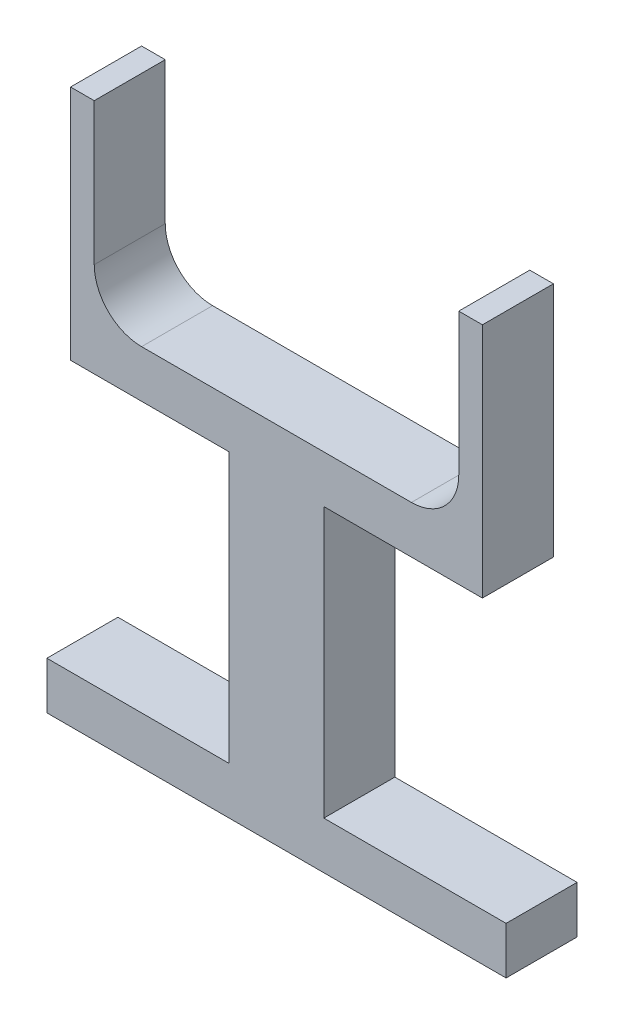
SolidWorks part; units mm, degrees
ref_plane "前基準面" through (0, 0, 0) normal (0, 0, 1) x (1, 0, 0)
ref_plane "上基準面" through (0, 0, 0) normal (0, 1, 0) x (1, 0, 0)
ref_plane "右基準面" through (0, 0, 0) normal (1, 0, 0) x (0, 0, -1)
sketch "草圖1" plane through (0, 0, 0) normal (0, 0, 1) x (1, 0, 0)
  line L1 (-77.3723, -11.2295) -> (19.6277, -11.2295)
  line L2 (-77.3723, -11.2295) -> (-77.3723, -21.2295)
  line L3 (-77.3723, -21.2295) -> (19.6277, -21.2295)
  line L4 (19.6277, -11.2295) -> (19.6277, -21.2295)
  line L5 (-38.8723, 45.7705) -> (-18.8723, 45.7705)
  line L6 (-38.8723, 45.7705) -> (-38.8723, -11.2295)
  line L7 (-38.8723, -11.2295) -> (-18.8723, -11.2295)
  line L8 (-18.8723, 45.7705) -> (-18.8723, -11.2295)
  line L9 (-72.3723, 55.7705) -> (14.6277, 55.7705)
  line L10 (-72.3723, 55.7705) -> (-72.3723, 45.7705)
  line L11 (-72.3723, 45.7705) -> (14.6277, 45.7705)
  line L12 (14.6277, 55.7705) -> (14.6277, 45.7705)
  line L13 (-72.3723, 55.7705) -> (-67.3723, 55.7705)
  line L14 (-72.3723, 55.7705) -> (-72.3723, 95.7705)
  line L15 (-72.3723, 95.7705) -> (-67.3723, 95.7705)
  line L16 (-67.3723, 55.7705) -> (-67.3723, 95.7705)
  line L17 (14.6277, 55.7705) -> (9.6277, 55.7705)
  line L18 (14.6277, 55.7705) -> (14.6277, 95.7705)
  line L19 (14.6277, 95.7705) -> (9.6277, 95.7705)
  line L20 (9.6277, 55.7705) -> (9.6277, 95.7705)
  dimension "D1" = 10
  dimension "D2" = 97
  dimension "D3" = 20
  dimension "D4" = 38.5
  dimension "D5" = 87
  dimension "D6" = 33.5
  dimension "D7" = 5
  dimension "D8" = 5
  dimension "D9" = 40
  dimension "D10" = 10
  dimension "D11" = 40
  dimension "D12" = 57
  dimension "D13" = 57
extrude "填料-伸長1" add sketch "草圖1" along normal blind 15 contours L9 L16 L15 L14 | L12 L9 L10 L11 L5 | L20 L9 L18 L19 | L8 L5 L6 L1 | L4 L1 L2 L3
fillet "圓角1" radius 10 2 edges at (9.6277, 55.7705, 7.5) (-67.3723, 55.7705, 7.5)
